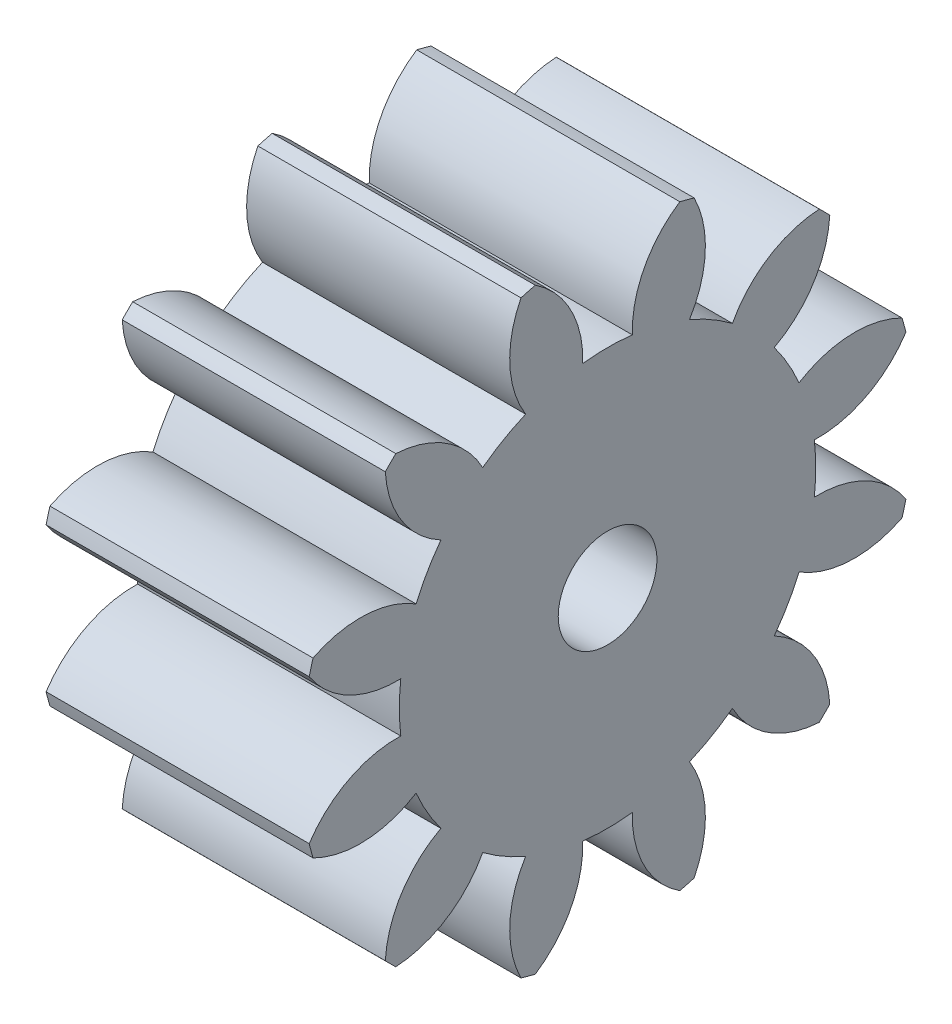
SolidWorks part; units mm, degrees
ref_plane "Plane1" through (0, 0, 0) normal (0, 0, 1) x (1, 0, 0)
ref_plane "Plane2" through (0, 0, 0) normal (0, 1, 0) x (1, 0, 0)
ref_plane "Plane3" through (0, 0, 0) normal (1, 0, 0) x (0, 0, -1)
sketch "HoldingSke" plane through (0, 0, 0) normal (0, 1, 0) x (1, 0, 0)
  line L0 (0, 0) -> (298.1394, -63.3715)
  line L1 (-15, 0) -> (100, 0) construction
  line L2 (0, 0) -> (-2.1039, 2.3779)
  line L3 (0, 0) -> (-11.863, 4.5341)
  line L4 (0, 0) -> (8.4473, 1.7955)
  line L5 (0, 0) -> (-47.5972, -17.7524)
  line L6 (0, 0) -> (-10.5278, -7.1032)
  line L7 (-2.1039, 2.3779) -> (8.8308, 51.9871)
  line L8 (-76.2, 54.61) -> (-71.1708, 54.61)
  line L9 (-71.009, 38.7566) -> (-53.1078, 45.2721)
  line L10 (-76.2, 71.12) -> (104.1128, 71.12)
  line L11 (0, 0) -> (-12.7, 0)
  line L12 (-76.2, 101.6) -> (-76.1147, 101.6)
  line L13 (24.9733, 27.94) -> (52.9518, 28.4284)
  line L14 (24.9733, 27.94) -> (24.9746, 27.94)
  line L15 (24.9733, 27.94) -> (100.4006, 29.5858)
  circle A0 centre (0, 0) radius 2.3812
  circle A1 centre (0, 0) radius 10.0529
  circle A2 centre (0, 0) radius 38.1
  circle A3 centre (0, 0) radius 2.3812
  dimension "MHD" = 20.1058
  dimension "Hub_dia" = 76.2
  dimension "Bore" = 4.7625
  dimension "MBD" = 4.7625
  dimension "Num_teeth" = 12
  dimension "Pitch" = 304.8
  dimension "Overall_len" = 50.8
  dimension "Show_teeth" = 12
  dimension "Thickness" = 12.7
  dimension "OAL" = 50.8001
  dimension "T_dim" = 5.0292
  dimension "Ap" = 20
  dimension "H" = 19.05
  dimension "Pitch_radius" = 180.3128
  dimension "Width" = 12.7
  dimension "Backlash" = 0.0853
  dimension "Addendum_fac" = 1
  dimension "Dedendum_fac" = 1.25
  dimension "Clearance_fac" = 0.25
  dimension "Dedendum_add" = 0.0013
sketch "BasProSke" plane through (0, 0, 0) normal (0, 1, 0) x (1, 0, 0)
  line L0 (-10, 0) -> (60, 0) construction
  line L1 (0, 0) -> (0, 14.8167)
  line L2 (0, 0) -> (12.7, 0)
  line L3 (12.7, 0) -> (12.7, 14.8167)
  line L4 (12.7, 14.8167) -> (0, 14.8167)
  dimension "Thickness" = 12.7
  dimension "Diameter" = 29.6333
revolve "Base-Revolve" add sketch "BasProSke" angle 360 about L0
sketch "TooCutSke" plane through (0, 0, 0) normal (1, 0, 0) x (0, 0, -1)
  line L1 (0, 0) -> (0, 107) construction
  line L2 (0, 0) -> (-1.8068, 12.5708) construction
  line L3 (0, 0) -> (-6.5275, 24.3609) construction
  line L4 (-1.8068, 12.5708) -> (-3.2637, 12.1804) construction
  arc A0 (1.1968, 9.9814) -> (-1.1968, 9.9814) centre (0, 0) ccw
  arc A1 (3.5177, 14.4192) -> (-3.5177, 14.4192) centre (0, 0) ccw
  circle A2 centre (0, 0) radius 12.7 construction
  circle A3 centre (0, 0) radius 11.9341 construction
  arc A4 (-1.1968, 9.9814) -> (-3.5177, 14.4192) centre (-6.2739, 10.1519) ccw
  arc A5 (3.5177, 14.4192) -> (1.1968, 9.9814) centre (6.2739, 10.1519) ccw
  dimension "Root_dia" = 20.1058
  dimension "Overcut_dia" = 29.6841
  dimension "Pitch_dia" = 25.4
  dimension "Base_dia" = 23.8682
  dimension "Flank_rad" = 5.08
  dimension "Half_ang" = 15
  dimension "Half_CT" = 1.5083
extrude "ToothCut" cut sketch "TooCutSke" along normal through all
fillet "Breaks" [suppressed] radius 0.0423
fillet "RootFillets" [suppressed] radius 0.5304
pattern_circular "TeethCuts" count 12 every 30 about axis through (-10, 0, 0) along (1, 0, 0) of "ToothCut", "RootFillets", "Breaks"
sketch "HubNeaOneSke" plane through (0, 0, 0) normal (-1, 0, 0) x (0, 0, 1)
  circle A0 centre (0, 0) radius 10.0529
  dimension "Diameter" = 20.1058
extrude "HubNearOne" [suppressed] add sketch "HubNeaOneSke" along normal blind 38.1001
sketch "HubNeaBotSke" plane through (0, 0, 0) normal (-1, 0, 0) x (0, 0, 1)
  circle A0 centre (0, 0) radius 10.0529
  dimension "Diameter" = 20.1058
extrude "HubNearBoth" [suppressed] add sketch "HubNeaBotSke" along normal blind 19.05
ref_plane "FarPln" through (12.7, 0, 0) normal (1, 0, 0) x (0, 0, -1)
sketch "HubFarSke" plane through (12.7, 0, 0) normal (1, 0, 0) x (0, 0, -1)
  circle A0 centre (0, 0) radius 10.0529
  dimension "Diameter" = 20.1058
extrude "HubFar" [suppressed] add sketch "HubFarSke" along normal blind 19.05
sketch "BorSke" plane through (0, 0, 0) normal (1, 0, 0) x (0, 0, -1)
  circle A0 centre (0, 0) radius 2.3812
  dimension "Diameter" = 4.7625
extrude "Bore" cut sketch "BorSke" along normal mid plane 101.6001
sketch "KeySke" plane through (0, 0, 0) normal (1, 0, 0) x (0, 0, -1)
  line L0 (-0.127, 0) -> (-0.127, 2.6479)
  line L1 (-0.127, 2.6479) -> (0.127, 2.6479)
  line L2 (0.127, 2.6479) -> (0.127, 0)
  line L3 (0, 0) -> (0, 34) construction
  line L4 (-0.127, 0) -> (0.127, 0)
  dimension "Offset" = 2.648
  dimension "Width" = 0.254
extrude "Keyway" [suppressed] cut sketch "KeySke" along normal mid plane 101.6001
pattern_circular "Keyway2" [suppressed] count 2 every 90 about axis through (-10, 0, 0) along (1, 0, 0)
equation "' \"Pitch@HoldingSke\" = 4"
equation "' \"Num_teeth@HoldingSke\" = 12"
equation "' \"Ap@HoldingSke\" =  20"
equation "' \"Ap@HoldingSke\" = 20"
equation "' \"Width@HoldingSke\" = 0.5"
equation "' \"Hub_dia@HoldingSke\"= 1"
equation "' \"Hub_dia@HoldingSke\" = 1"
equation "' \"Overall_len@HoldingSke\" = 1.0"
equation "' \"Bore@HoldingSke\" = 0.75"
equation "' \"T_dim@HoldingSke\" = 0.85"
equation "' \"Width@KeySke\" = 0.25"
equation "' \"Show_teeth@HoldingSke\" = 13"
equation "' \"Backlash@HoldingSke\" = 0.009"
equation "' \"Addendum_fac@HoldingSke\" = 1.0"
equation "' \"Dedendum_fac@HoldingSke\" = 1.25"
equation "' \"Dedendum_add@HoldingSke\" = 0.00005"
equation "' \"Clearance_fac@HoldingSke\" = 0.25"
equation "' \"Pitch@HoldingSke\" = 0.5"
equation "' \"Num_teeth@HoldingSke\" = 23"
equation "' \"Show_teeth@HoldingSke\" = 23"
equation "' \"Backlash@HoldingSke\" = 0.0375"
equation "\"Overcut_dia@TooCutSke\" = (\"Num_teeth@HoldingSke\" + 2 * \"Addendum_fac@HoldingSke\") / \"Pitch@HoldingSke\" + 0.002"
equation "\"Pitch_dia@TooCutSke\" = \"Num_teeth@HoldingSke\" / \"Pitch@HoldingSke\""
equation "\"Base_dia@TooCutSke\" = \"Num_teeth@HoldingSke\" / \"Pitch@HoldingSke\" * cos((\"Ap@HoldingSke\"  * 3.14159265 / 180))"
equation "\"Root_dia@TooCutSke\" = (\"Num_teeth@HoldingSke\" + 2) / \"Pitch@HoldingSke\" - 2 * (\"Addendum_fac@HoldingSke\" + \"Dedendum_fac@HoldingSke\") / \"Pitch@HoldingSke\" - \"Dedendum_add@HoldingSke\" * 2"
equation "\"Half_ang@TooCutSke\" = 180 / \"Num_teeth@HoldingSke\""
equation "\"Half_CT@TooCutSke\" = \"Num_teeth@HoldingSke\" / \"Pitch@HoldingSke\" * sin((3.14159265 / 2 / \"Num_teeth@HoldingSke\")) / 2 - 7 * \"Backlash@HoldingSke\" / 4"
equation "\"Flank_rad@TooCutSke\" = \"Num_teeth@HoldingSke\" / \"Pitch@HoldingSke\" / 5"
equation "\"Radius@RootFillets\" = \"Clearance_fac@HoldingSke\" / \"Pitch@HoldingSke\" + \"Dedendum_add@HoldingSke\""
equation "\"Break_rad@Breaks\" = 0.02 / \"Pitch@HoldingSke\""
equation "\"Thickness@HoldingSke\" = \"Width@HoldingSke\""
equation "\"OAL@HoldingSke\" = \"Thickness@HoldingSke\""
equation "\"MHD@HoldingSke\" = (\"Num_teeth@HoldingSke\" + 2) / \"Pitch@HoldingSke\" - 2 * (\"Addendum_fac@HoldingSke\" + \"Dedendum_fac@HoldingSke\")  / \"Pitch@HoldingSke\" - \"Dedendum_add@HoldingSke\" * 2"
equation "\"MBD@HoldingSke\" = (\"Num_teeth@HoldingSke\" + 2) / \"Pitch@HoldingSke\" - 2 * (\"Addendum_fac@HoldingSke\" + \"Dedendum_fac@HoldingSke\")  / \"Pitch@HoldingSke\" - \"Dedendum_add@HoldingSke\" * 2 - 0.002"
equation "\"MHD@HoldingSke\" = ((sgn( \"MHD@HoldingSke\" - \"Hub_dia@HoldingSke\" )-1)*( \"MHD@HoldingSke\" - \"Hub_dia@HoldingSke\" ))/-2+ \"Hub_dia@HoldingSke\""
equation "\"MBD@HoldingSke\" = ((sgn( \"MBD@HoldingSke\" - \"Bore@HoldingSke\" )-1)*( \"MBD@HoldingSke\" - \"Bore@HoldingSke\" ))/-2+ \"Bore@HoldingSke\""
equation "\"OAL@HoldingSke\" = ((sgn( \"OAL@HoldingSke\" - \"Overall_len@HoldingSke\" )+1)*( \"OAL@HoldingSke\" - \"Overall_len@HoldingSke\" ))/2 + \"Overall_len@HoldingSke\" + 0.000002"
equation "\"Num_teeth@TeethCuts\" = int( \"Show_teeth@HoldingSke\" ) + 1"
equation "\"Num_teeth@TeethCuts\" = ((sgn( \"Num_teeth@TeethCuts\" - \"Num_teeth@HoldingSke\" )-1)*( \"Num_teeth@TeethCuts\" - \"Num_teeth@HoldingSke\" ))/-2+ \"Num_teeth@HoldingSke\""
equation "\"Num_teeth@TeethCuts\" = ((sgn( \"Num_teeth@TeethCuts\" - 2.0)+1)*( \"Num_teeth@TeethCuts\" - 2.0))/2 +2.0"
equation "\"Angle@TeethCuts\" = 360.0 / \"Num_teeth@HoldingSke\""
equation "\"Diameter@BasProSke\" = (\"Num_teeth@HoldingSke\" + 2 * \"Addendum_fac@HoldingSke\") / \"Pitch@HoldingSke\""
equation "\"Thickness@BasProSke\"  = \"Thickness@HoldingSke\""
equation "' \"Fillet_rad@BasProSke\" =  \"Thickness@HoldingSke\" * 0.05"
equation "' \"Fillet_rad@BasProSke\" = \"Thickness@HoldingSke\" * 0.05"
equation "\"MHD@HoldingSke\" = ((sgn( \"MHD@HoldingSke\" - \"Root_dia@TooCutSke\" )-1)*( \"MHD@HoldingSke\" - \"Root_dia@TooCutSke\" ))/-2+ \"Root_dia@TooCutSke\""
equation "\"Diameter@HubNeaOneSke\" = \"MHD@HoldingSke\""
equation "\"Length@HubNearOne\" = \"OAL@HoldingSke\" - \"Thickness@BasProSke\""
equation "\"Diameter@HubNeaBotSke\" = \"MHD@HoldingSke\""
equation "\"Length@HubNearBoth\" = ( \"OAL@HoldingSke\" - \"Thickness@BasProSke\" ) / 2.0"
equation "\"Thickness@FarPln\" = \"Thickness@BasProSke\""
equation "\"Diameter@HubFarSke\" = \"MHD@HoldingSke\""
equation "\"Length@HubFar\" = ( \"OAL@HoldingSke\" - \"Thickness@BasProSke\" ) / 2.0"
equation "\"Diameter@BorSke\" = \"MBD@HoldingSke\""
equation "\"D1@Bore\" = \"OAL@HoldingSke\" * 2.0"
equation "\"D1@Keyway\" = \"OAL@HoldingSke\" * 2.0"
equation "\"Offset@KeySke\" = \"T_dim@HoldingSke\" - \"MBD@HoldingSke\" / 2.0"
